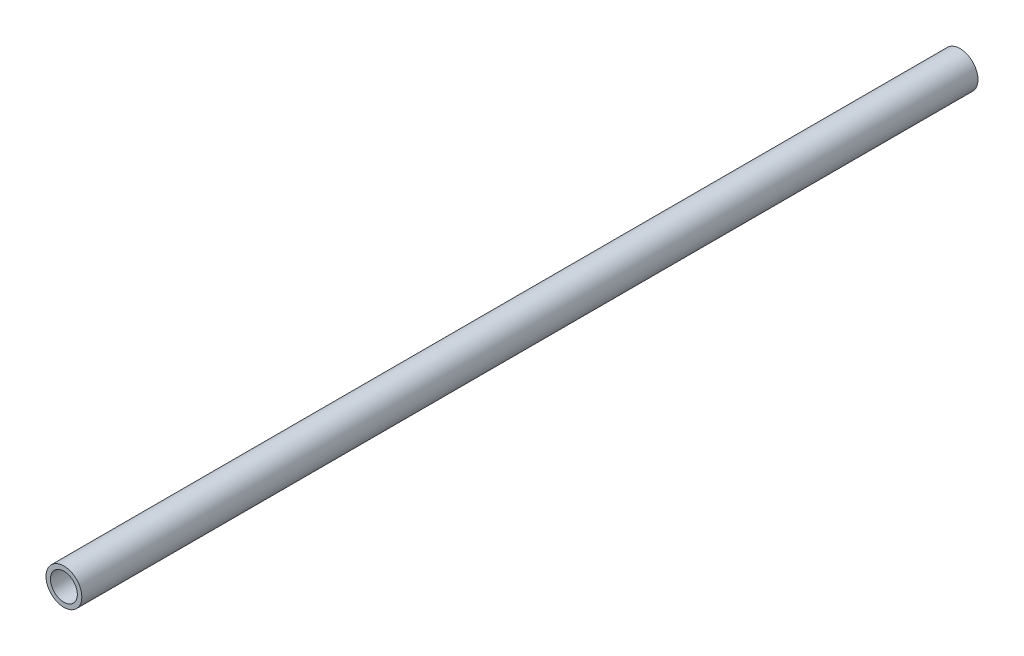
SolidWorks part; units mm, degrees
material "Hexcel AS4C (3000 Filaments)"
ref_plane "Front Plane" through (0, 0, 0) normal (0, 0, 1) x (1, 0, 0)
ref_plane "Top Plane" through (0, 0, 0) normal (0, 1, 0) x (1, 0, 0)
ref_plane "Right Plane" through (0, 0, 0) normal (1, 0, 0) x (0, 0, -1)
sketch "Sketch1" plane through (0, 0, 0) normal (0, 0, 1) x (1, 0, 0)
  circle A0 centre (0, 0) radius 12.7
  circle A1 centre (0, 0) radius 9.525
  dimension "D1" = 25.4
  dimension "D2" = 19.05
extrude "Boss-Extrude1" add sketch "Sketch1" along normal blind 635
